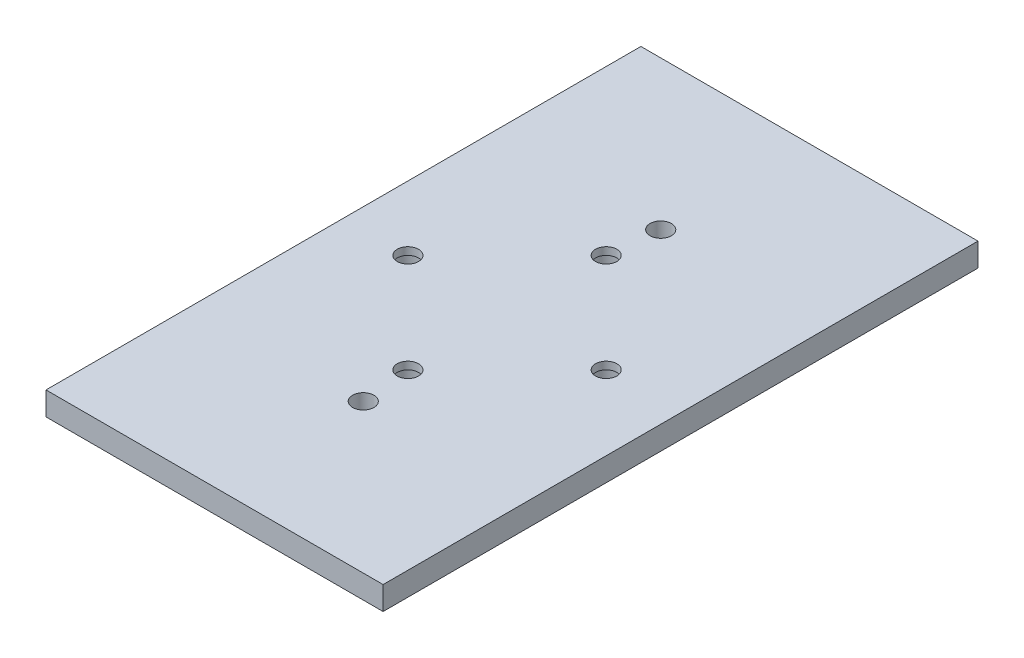
SolidWorks part; units mm, degrees
ref_plane "Front Plane" through (0, 0, 0) normal (0, 0, 1) x (1, 0, 0)
ref_plane "Top Plane" through (0, 0, 0) normal (0, 1, 0) x (1, 0, 0)
ref_plane "Right Plane" through (0, 0, 0) normal (1, 0, 0) x (0, 0, -1)
sketch "Sketch2" plane through (0, 0, 0) normal (0, 1, 0) x (1, 0, 0)
  line L2 (0, 0) -> (0, 152.4)
  line L4 (88.9, 0) -> (88.9, 152.4)
  line L10 (-1000, 76.2) -> (49000, 76.2) construction
  line L13 (0, 152.4) -> (88.9, 152.4)
  line L14 (0, 0) -> (88.9, 0)
  point P11 (0, 76.2)
  dimension "D1" = 152.4
  dimension "D2" = 88.9
extrude "Boss-Extrude1" add sketch "Sketch2" along normal blind 5.9944 contours L4 L13 L2 L14
sketch "Sketch4" plane through (0, 5.9944, 0) normal (0, 1, 0) x (1, 0, 0)
  line L0 (0, 0) -> (0, 152.4) construction
  line L2 (45.72, 114.3) -> (45.72, 38.1) construction
  line L3 (0, 0) -> (0, 152.4) construction
  circle A0 centre (45.72, 114.3) radius 2.7305
  circle A1 centre (45.72, 38.1) radius 2.7305
  point P4 (45.72, 76.2)
  point P10 (0, 76.2)
  dimension "D3" = 5.461
  dimension "D4" = 5.461
  dimension "D1" = 76.2
  dimension "D2" = 45.72
extrude "Cut-Extrude2" cut sketch "Sketch4" against normal through all both
sketch "Sketch5" plane through (0, 5.9944, 0) normal (0, 1, 0) x (1, 0, 0)
  line L0 (44.45, 101.6) -> (44.45, 50.8) construction
  line L6 (88.9, 0) -> (88.9, 152.4) construction
  line L7 (19.05, 76.2) -> (69.85, 76.2) construction
  line L8 (0, 152.4) -> (88.9, 152.4) construction
  circle A0 centre (69.85, 76.2) radius 2.7305
  circle A1 centre (19.05, 76.2) radius 2.7305
  circle A2 centre (44.45, 101.6) radius 2.7305
  circle A3 centre (44.45, 50.8) radius 2.7305
  point P6 (44.45, 152.4)
  point P9 (88.9, 76.2)
  point P10 (44.45, 76.2)
  point P15 (44.45, 102.8708)
  point P16 (44.45, 122.2678)
  point P17 (0, 0)
  point P18 (44.45, 76.2)
  dimension "D1" = 5.461
  dimension "D2" = 5.461
  dimension "D4" = 5.461
  dimension "D5" = 5.461
  dimension "D3" = 50.8
  dimension "D6" = 50.8
extrude "Cut-Extrude3" cut sketch "Sketch5" against normal through all both and the other way through all
sketch "Sketch7" plane through (0, 5.9944, 0) normal (0, 1, 0) x (1, 0, 0)
  line L0 (0, 0) -> (88.9, 0) construction
  line L1 (0, 152.4) -> (2.54, 152.4)
  line L2 (0, 152.4) -> (0, 0)
  line L3 (0, 0) -> (2.54, 0)
  line L4 (2.54, 152.4) -> (2.54, 0)
  dimension "D1" = 2.54
extrude "Cut-Extrude5" cut sketch "Sketch7" against normal through all both and the other way through all
sketch "Sketch8" plane through (0, 0, 0) normal (0, -1, 0) x (1, 0, 0)
  circle A0 centre (19.05, -76.2) radius 3.683
  circle A1 centre (44.45, -50.8) radius 3.683
  circle A2 centre (69.85, -76.2) radius 3.683
  circle A3 centre (44.45, -101.6) radius 3.683
  dimension "D1" = 7.366
  dimension "D2" = 7.366
  dimension "D3" = 7.366
  dimension "D4" = 7.366
extrude "Cut-Extrude6" cut sketch "Sketch8" against normal blind 4.064
equation "\"threaded_insert_hole\"=0.1472"
equation "\"th\"=1.25249"
